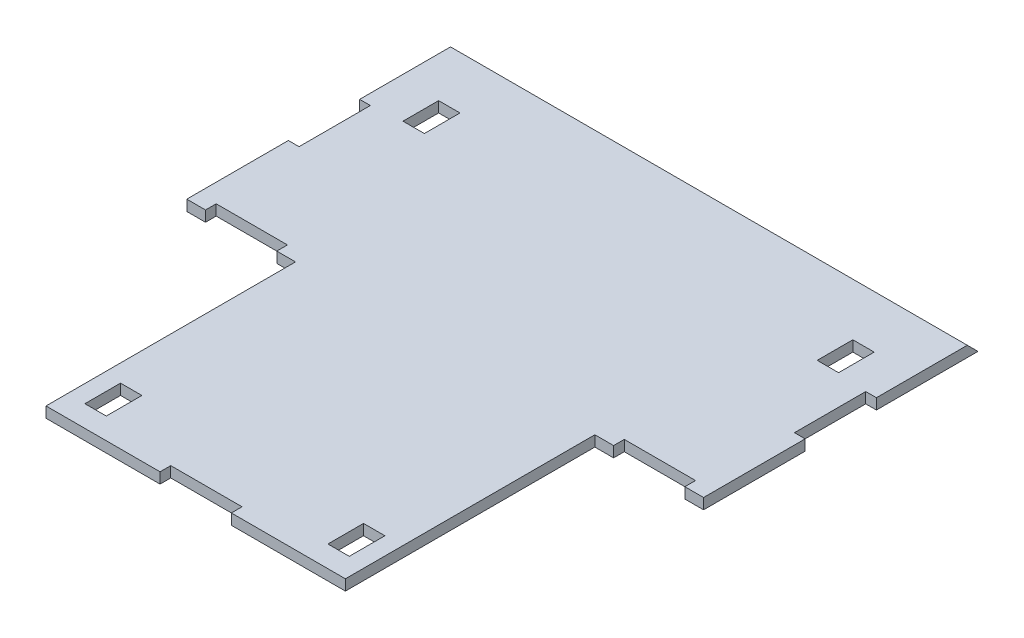
SolidWorks part; units mm, degrees
ref_plane "Alzado" through (0, 0, 0) normal (0, 0, 1) x (1, 0, 0)
ref_plane "Planta" through (0, 0, 0) normal (0, 1, 0) x (1, 0, 0)
ref_plane "Vista lateral" through (0, 0, 0) normal (1, 0, 0) x (0, 0, -1)
sketch "Croquis1" plane through (0, 0, 0) normal (0, 1, 0) x (1, 0, 0)
  line L1 (-72.5, 73.5) -> (72.5, 73.5)
  line L2 (-72.5, 73.5) -> (-72.5, -73.5)
  line L3 (-72.5, -73.5) -> (72.5, -73.5)
  line L4 (72.5, 73.5) -> (72.5, -73.5)
  line L5 (-72.5, 73.5) -> (72.5, -73.5) construction
  line L6 (-72.5, -73.5) -> (72.5, 73.5) construction
  line L7 (-42, -73.5) -> (42, -73.5)
  line L8 (-42, -73.5) -> (-42, -3.5)
  line L9 (-42, -3.5) -> (42, -3.5)
  line L10 (42, -73.5) -> (42, -3.5)
  line L11 (-42, -3.5) -> (-72.5, -3.5)
  line L12 (-42, -3.5) -> (-42, -73.5)
  line L13 (-42, -73.5) -> (-72.5, -73.5)
  line L14 (-72.5, -3.5) -> (-72.5, -73.5)
  line L15 (42, -3.5) -> (72.5, -3.5)
  line L16 (42, -3.5) -> (42, -73.5)
  line L17 (42, -73.5) -> (72.5, -73.5)
  line L18 (72.5, -3.5) -> (72.5, -73.5)
  point P0 (0, 0)
  dimension "D1" = 145
  dimension "D2" = 147
  dimension "D3" = 84
  dimension "D4" = 30.5
  dimension "D5" = 70
extrude "Saliente-Extruir1" add sketch "Croquis1" along normal blind 3 contours L9 L15 L4 L1 L2 L11 | L3 L10 L9 L8
sketch "Croquis2" plane through (0, 3, 0) normal (0, 1, 0) x (1, 0, 0)
  line L0 (-42, -73.5) -> (-42, -3.5) construction
  line L1 (-37.09, -67.5) -> (-31.09, -67.5)
  line L2 (-37.09, -67.5) -> (-37.09, -57.5)
  line L3 (-37.09, -57.5) -> (-31.09, -57.5)
  line L4 (-31.09, -67.5) -> (-31.09, -57.5)
  line L5 (-42, -73.5) -> (42, -73.5) construction
  line L6 (0, 0) -> (0, -67.5) construction
  line L7 (37.09, -57.5) -> (31.09, -57.5)
  line L8 (31.09, -67.5) -> (31.09, -57.5)
  line L9 (37.09, -67.5) -> (31.09, -67.5)
  line L10 (37.09, -67.5) -> (37.09, -57.5)
  line L11 (-72.5, 73.5) -> (72.5, 73.5) construction
  line L12 (-61.11, 55.77) -> (-55.11, 55.77)
  line L13 (-61.11, 55.77) -> (-61.11, 45.77)
  line L14 (-61.11, 45.77) -> (-55.11, 45.77)
  line L15 (-55.11, 55.77) -> (-55.11, 45.77)
  line L16 (-72.5, 73.5) -> (-72.5, -3.5) construction
  line L17 (61.11, 45.77) -> (55.11, 45.77)
  line L18 (55.11, 55.77) -> (55.11, 45.77)
  line L19 (61.11, 55.77) -> (55.11, 55.77)
  line L20 (61.11, 55.77) -> (61.11, 45.77)
  point P21 (-61.11, 50.77)
  dimension "D1" = 4.91
  dimension "D2" = 10
  dimension "D3" = 6
  dimension "D4" = 6
  dimension "D5" = 17.73
  dimension "D6" = 11.39
  dimension "D7" = 6
  dimension "D8" = 10
extrude "Cortar-Extruir1" cut sketch "Croquis2" against normal blind 3
sketch "Croquis3" plane through (0, 3, 0) normal (0, 1, 0) x (1, 0, 0)
  line L0 (0, 0) -> (0, -59.7652) construction
  line L1 (-42, -73.5) -> (42, -73.5) construction
  line L2 (-10, -73.5) -> (10, -73.5)
  line L3 (-10, -73.5) -> (-10, -70.5)
  line L4 (-10, -70.5) -> (10, -70.5)
  line L5 (10, -73.5) -> (10, -70.5)
  line L6 (-72.5, 35) -> (72.5, 35) construction
  line L7 (-72.5, 73.5) -> (-72.5, -3.5) construction
  line L8 (72.5, 73.5) -> (72.5, -3.5) construction
  line L9 (72.5, 25) -> (69.5, 25)
  line L10 (-72.5, 45) -> (-69.5, 45)
  line L11 (-72.5, 45) -> (-72.5, 25)
  line L12 (-72.5, 25) -> (-69.5, 25)
  line L13 (-69.5, 45) -> (-69.5, 25)
  line L14 (69.5, 45) -> (69.5, 25)
  line L15 (72.5, 45) -> (69.5, 45)
  line L16 (72.5, 45) -> (72.5, 25)
  line L17 (-57.25, -3.5) -> (-57.25, 25) construction
  line L18 (-72.5, -3.5) -> (-42, -3.5) construction
  line L19 (67.25, -0.5) -> (47.25, -0.5)
  line L20 (-67.25, -3.5) -> (-47.25, -3.5)
  line L21 (-67.25, -3.5) -> (-67.25, -0.5)
  line L22 (-67.25, -0.5) -> (-47.25, -0.5)
  line L23 (-47.25, -3.5) -> (-47.25, -0.5)
  line L24 (47.25, -3.5) -> (47.25, -0.5)
  line L25 (67.25, -3.5) -> (47.25, -3.5)
  line L26 (67.25, -3.5) -> (67.25, -0.5)
  dimension "D1" = 20
  dimension "D2" = 3
  dimension "D3" = 10
  dimension "D4" = 20
  dimension "D5" = 3
  dimension "D6" = 10
  dimension "D7" = 20
  dimension "D8" = 3
  dimension "D9" = 10
extrude "Cortar-Extruir2" cut sketch "Croquis3" against normal blind 3
sketch "Croquis5" plane through (72.5, 0, 0) normal (1, 0, 0) x (0, 0, -1)
  line L0 (73.5, 0) -> (70.5, 3)
  line L1 (73.5, 3) -> (45, 3) construction
  line L2 (70.5, 3) -> (73.5, 3)
  line L3 (73.5, 3) -> (73.5, 0)
extrude "Cortar-Extruir3" cut sketch "Croquis5" against normal through all
